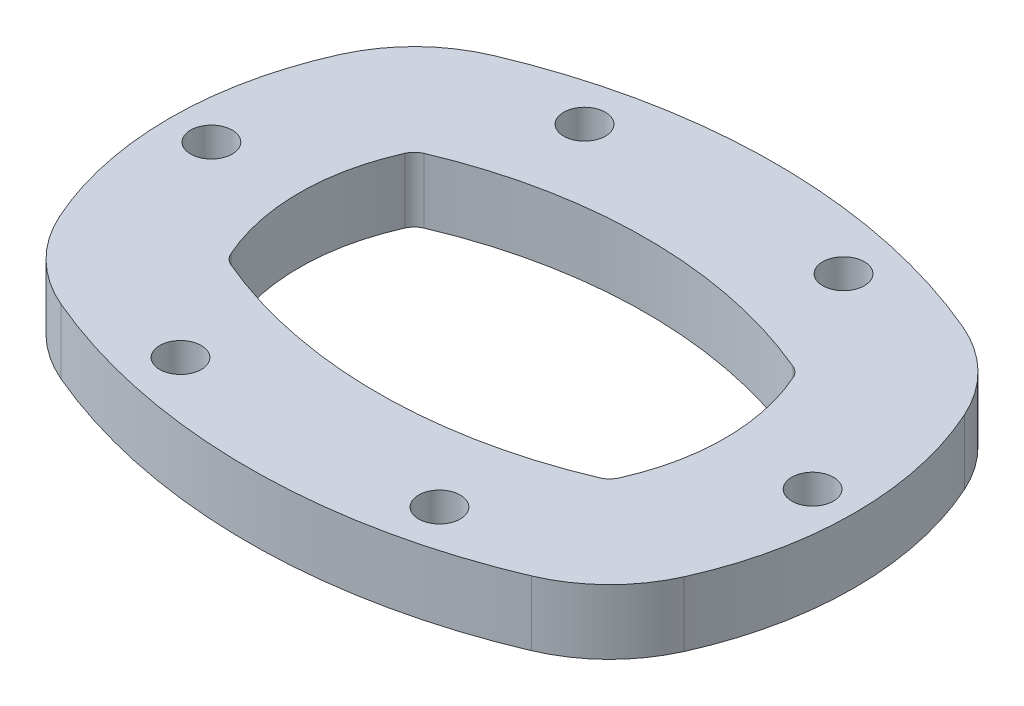
SolidWorks part; units mm, degrees
ref_plane "Front Plane" through (0, 0, 0) normal (0, 0, 1) x (1, 0, 0)
ref_plane "Top Plane" through (0, 0, 0) normal (0, 1, 0) x (1, 0, 0)
ref_plane "Right Plane" through (0, 0, 0) normal (1, 0, 0) x (0, 0, -1)
sketch "Sketch1" plane through (0, 0, 0) normal (0, 1, 0) x (1, 0, 0)
  line L0 (-73.025, 0) -> (73.025, 0) construction
  line L1 (0, 0) -> (0, 46.0375) construction
  arc A0 (-66.6217, -29.9031) -> (-66.6217, 29.9031) centre (0, 0) cw
  arc A1 (63.3113, 33.1473) -> (-63.3113, 33.1473) centre (0, -115.8875) ccw
  arc A2 (-66.6217, 29.9031) -> (-63.3113, 33.1473) centre (-60.8285, 27.3028) cw
  arc A3 (63.3113, -33.1473) -> (-63.3113, -33.1473) centre (0, 115.8875) cw
  arc A4 (-66.6217, -29.9031) -> (-63.3113, -33.1473) centre (-60.8285, -27.3028) ccw
  arc A5 (66.6217, -29.9031) -> (63.3113, -33.1473) centre (60.8285, -27.3028) cw
  arc A6 (66.6217, 29.9031) -> (63.3113, 33.1473) centre (60.8285, 27.3028) ccw
  arc A7 (66.6217, -29.9031) -> (66.6217, 29.9031) centre (0, 0) ccw
  arc A8 (80.6909, 74.0588) -> (-80.6909, 74.0588) centre (0, -115.8875) ccw
  arc A9 (-107.1741, 48.105) -> (-80.6909, 74.0588) centre (-60.8285, 27.3028) cw
  arc A10 (-107.1741, -48.105) -> (-107.1741, 48.105) centre (0, 0) cw
  arc A11 (-107.1741, -48.105) -> (-80.6909, -74.0588) centre (-60.8285, -27.3028) ccw
  arc A12 (80.6909, -74.0588) -> (-80.6909, -74.0588) centre (0, 115.8875) cw
  arc A13 (107.1741, -48.105) -> (80.6909, -74.0588) centre (60.8285, -27.3028) cw
  arc A14 (107.1741, -48.105) -> (107.1741, 48.105) centre (0, 0) ccw
  arc A15 (107.1741, 48.105) -> (80.6909, 74.0588) centre (60.8285, 27.3028) ccw
  circle A16 centre (-103.1875, 0) radius 7.1438
  circle A17 centre (-44.45, 69.3541) radius 7.1437
  arc A18 (-44.45, 69.3541) -> (44.45, 69.3541) centre (0, -115.8875) cw construction
  circle A19 centre (103.1875, 0) radius 7.1438
  circle A20 centre (44.45, 69.3541) radius 7.1437
  circle A21 centre (-44.45, -69.3541) radius 7.1437
  circle A22 centre (44.45, -69.3541) radius 7.1437
  arc A23 (-44.45, -69.3541) -> (44.45, -69.3541) centre (0, 115.8875) ccw construction
  dimension "D1" = 115.8875
  dimension "D2" = 161.925
  dimension "D3" = 73.025
  dimension "D4" = 6.35
  dimension "D6" = 14.2875
  dimension "D7" = 103.1875
  dimension "D8" = 190.5
  dimension "D5" = 44.45
  dimension "D9" = 44.45
extrude "Boss-Extrude1" add sketch "Sketch1" along normal blind 22.225
ref_plane "Plane1" through (0, -9.525, 0) normal (0, -1, 0) x (-1, 0, 0)
sketch "Sketch10" plane through (0, -9.525, 0) normal (0, -1, 0) x (-1, 0, 0)
  line L1 (0, -46.0375) -> (0, 46.0375)
  line L2 (0, 58.7375) -> (0, 46.0375)
  line L3 (0, -46.0375) -> (0, -58.7375)
  arc A0 (66.6217, -29.9031) -> (66.6217, 29.9031) centre (0, 0) ccw construction
  arc A1 (0, 46.0375) -> (63.3113, 33.1473) centre (0, -115.8875) cw construction
  arc A2 (66.6217, 29.9031) -> (63.3113, 33.1473) centre (60.8285, 27.3028) ccw construction
  arc A3 (66.6217, -29.9031) -> (63.3113, -33.1473) centre (60.8285, -27.3028) cw construction
  arc A4 (0, -46.0375) -> (63.3113, -33.1473) centre (0, 115.8875) ccw construction
  arc A5 (0, 58.7375) -> (68.2769, 44.8363) centre (0, -115.8875) cw
  arc A6 (78.2081, 35.1036) -> (68.2769, 44.8363) centre (60.8285, 27.3028) ccw
  arc A7 (78.2081, -35.1036) -> (78.2081, 35.1036) centre (0, 0) ccw
  arc A8 (78.2081, -35.1036) -> (68.2769, -44.8363) centre (60.8285, -27.3028) cw
  arc A9 (0, -58.7375) -> (68.2769, -44.8363) centre (0, 115.8875) ccw
  arc A10 (-63.3113, -33.1473) -> (63.3113, -33.1473) centre (0, 115.8875) ccw construction
  arc A12 (63.3113, -33.1473) -> (66.6217, -29.9031) centre (60.8285, -27.3028) ccw construction
  dimension "D1" = 73.025
  dimension "D2" = 115.8875
  dimension "D3" = 161.925
  dimension "D4" = 6.35
  dimension "D5" = 12.7
sketch "Sketch11" plane through (0, -9.525, 0) normal (0, -1, 0) x (-1, 0, 0)
  line L0 (0, 58.7375) -> (0, 46.0375)
  line L1 (0, -46.0375) -> (0, -58.7375)
  line L2 (-12.7, -58.2751) -> (-12.7, -58.7375) construction
  line L3 (0, -46.0375) -> (0, 46.0375)
  line L4 (-12.7, 58.7375) -> (-12.7, 58.2751) construction
  arc A0 (-63.3113, -33.1473) -> (63.3113, -33.1473) centre (0, 115.8875) ccw construction
  arc A1 (-66.6217, -29.9031) -> (-63.3113, -33.1473) centre (-60.8285, -27.3028) ccw construction
  arc A2 (-66.6217, 29.9031) -> (-66.6217, -29.9031) centre (0, 0) ccw construction
  arc A3 (-63.3113, 33.1473) -> (-66.6217, 29.9031) centre (-60.8285, 27.3028) ccw construction
  arc A4 (63.3113, 33.1473) -> (-63.3113, 33.1473) centre (0, -115.8875) ccw construction
  arc A5 (-63.3113, -33.1473) -> (0, -46.0375) centre (0, 115.8875) ccw construction
  arc A6 (-66.6217, -29.9031) -> (-63.3113, -33.1473) centre (-60.8285, -27.3028) ccw construction
  arc A7 (-66.6217, 29.9031) -> (-66.6217, -29.9031) centre (0, 0) ccw construction
  arc A8 (-63.3113, 33.1473) -> (-66.6217, 29.9031) centre (-60.8285, 27.3028) ccw construction
  arc A9 (0, 46.0375) -> (-63.3113, 33.1473) centre (0, -115.8875) ccw construction
  arc A10 (-12.7, 58.2751) -> (-68.2769, 44.8363) centre (0, -115.8875) ccw
  arc A11 (-68.2769, 44.8363) -> (-78.2081, 35.1036) centre (-60.8285, 27.3028) ccw
  arc A12 (-78.2081, 35.1036) -> (-78.2081, -35.1036) centre (0, 0) ccw
  arc A13 (-78.2081, -35.1036) -> (-68.2769, -44.8363) centre (-60.8285, -27.3028) ccw
  arc A14 (-68.2769, -44.8363) -> (-12.7, -58.2751) centre (0, 115.8875) ccw
  arc A15 (-12.7, 58.2751) -> (0, 58.7375) centre (0, -115.8875) cw
  arc A16 (-12.7, -58.2751) -> (0, -58.7375) centre (0, 115.8875) ccw
  dimension "D1" = 12.7
sketch "Sketch13" plane through (0, 0, 0) normal (1, 0, 0) x (0, 0, -1)
  line L0 (-35.1036, -9.525) -> (35.1036, -9.525) construction
  line L1 (-46.0375, -9.525) -> (-33.1473, -9.525) construction
  line L2 (44.8363, -9.525) -> (58.7375, -9.525) construction
  line L3 (58.7375, -9.525) -> (46.0375, -9.525)
  line L4 (-46.0375, 0) -> (46.0375, 0) construction
  line L5 (-48.105, 0) -> (48.105, 0) construction
  line L6 (-46.0375, -9.525) -> (-58.7375, -9.525) construction
  line L7 (-46.0375, -9.525) -> (-58.7404, -9.525)
  line L8 (58.7375, -9.525) -> (46.0375, -9.525) construction
  line L9 (-48.105, 0) -> (48.105, 0) construction
  line L10 (-46.0375, -9.525) -> (46.0375, -9.525)
  arc A0 (0, 63.5) -> (-35.9902, 54.0152) centre (0, -9.525) ccw construction
  arc A1 (-46.0375, -9.525) -> (-39.0022, 50.1036) centre (169.81, -4.7625) cw construction
  arc A2 (-35.9902, 54.0152) -> (-39.0022, 50.1036) centre (-32.8607, 48.4899) ccw construction
  arc A4 (-42.2494, 65.0656) -> (-51.2853, 53.3311) centre (-32.8607, 48.4899) ccw
  arc A5 (-58.7404, -9.525) -> (-51.2853, 53.3311) centre (169.81, -4.7625) cw
  arc A6 (58.7375, -9.525) -> (51.2853, 53.3311) centre (-169.8127, -4.7522) ccw
  arc A7 (46.0375, -9.525) -> (39.0022, 50.1036) centre (-169.81, -4.7625) ccw construction
  arc A8 (42.2504, 65.0651) -> (51.2853, 53.3311) centre (32.8625, 48.4913) cw
  arc A10 (35.9902, 54.0152) -> (39.0022, 50.1036) centre (32.8607, 48.4899) cw construction
  arc A11 (0, 63.5) -> (35.9902, 54.0152) centre (0, -9.525) cw construction
  arc A12 (-58.7344, -9.8051) -> (-51.2853, 53.3311) centre (169.81, -4.7625) cw construction
  arc A13 (0, 76.2) -> (-42.2494, 65.0656) centre (0, -9.525) ccw construction
  arc A14 (-42.2494, 65.0656) -> (42.2504, 65.0651) centre (0, -9.525) cw
  dimension "D1" = 73.025
  dimension "D2" = 215.9
  dimension "D3" = 6.35
  dimension "D5" = 85.725
  dimension "D6" = 46.0375
  dimension "D7" = 12.7
  dimension "D8" = 6.35
  dimension "D4" = 12.7
  dimension "D9" = 12.7
sketch "Sketch15" plane through (0, 0, 0) normal (0, 0, 1) x (1, 0, 0)
  line L0 (-85.725, -9.525) -> (-78.2081, -9.525) construction
  line L1 (78.2081, -9.525) -> (85.725, -9.525) construction
  arc A0 (-85.725, -9.525) -> (85.725, -9.525) centre (0, -9.525) cw
  point P3 (-98.44, -9.525)
  point P9 (0, 0)
  point P13 (-184.0973, 81.654)
  point P14 (0, 76.2)
